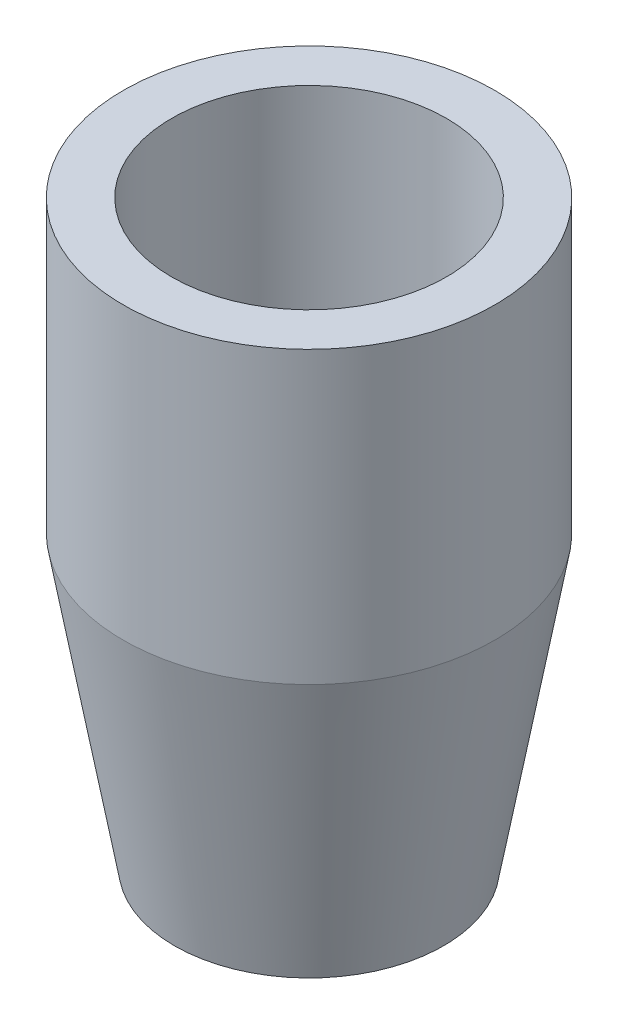
SolidWorks part; units mm, degrees
ref_plane "Front Plane" through (0, 0, 0) normal (0, 0, 1) x (1, 0, 0)
ref_plane "Top Plane" through (0, 0, 0) normal (0, 1, 0) x (1, 0, 0)
ref_plane "Right Plane" through (0, 0, 0) normal (1, 0, 0) x (0, 0, -1)
sketch "Sketch2" plane through (0, 0, 0) normal (0, 0, 1) x (1, 0, 0)
  line L0 (0, 0) -> (19.05, 0)
  line L1 (19.05, 0) -> (32.4861, 76.2)
  line L2 (32.4861, 76.2) -> (32.4861, 152.4)
  line L3 (32.4861, 152.4) -> (19.7861, 152.4)
  line L6 (0, 0) -> (0, 50.8)
  line L8 (-16.2819, 0) -> (-16.2819, 152.4) construction
  line L9 (19.7861, 152.4) -> (19.7861, 76.2)
  line L10 (19.7861, 76.2) -> (13.4361, 76.2)
  line L11 (13.4361, 76.2) -> (0, 50.8)
  line L12 (19.05, 0) -> (126.9814, 0) construction
  line L13 (13.4361, 76.2) -> (-18.7115, 76.2) construction
  dimension "D1" = 152.4
  dimension "D2" = 76.2
  dimension "D3" = 48.768
  dimension "D4" = 80
  dimension "D5" = 19.05
  dimension "D6" = 12.7
  dimension "D7" = 6.35
  dimension "D8" = 50.8
revolve "Revolve2" add sketch "Sketch2" angle 360 about L8
